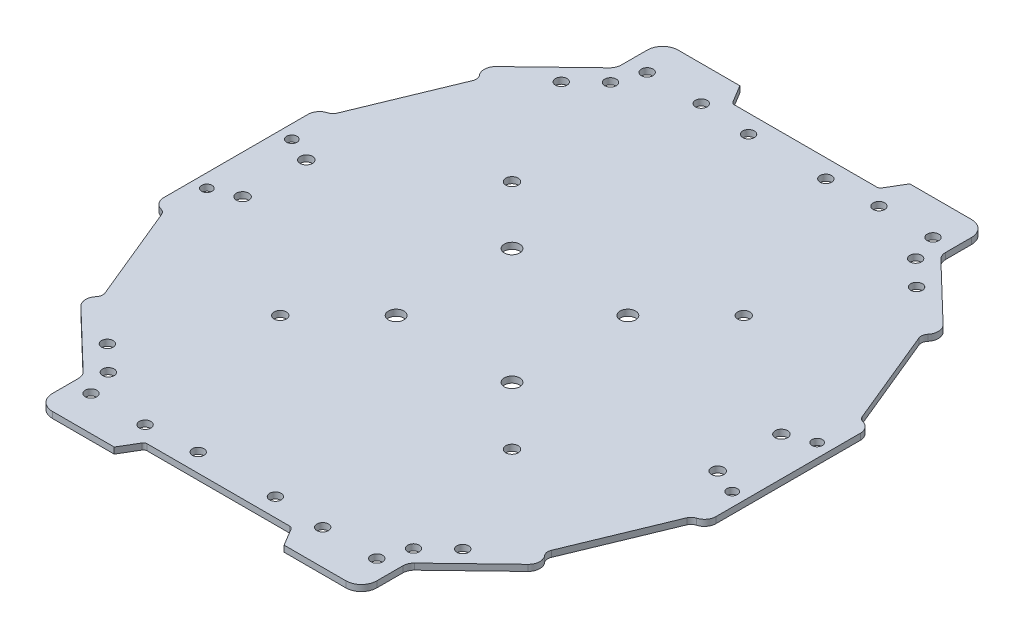
SolidWorks part; units mm, degrees
ref_plane "Front Plane" through (0, 0, 0) normal (0, 0, 1) x (1, 0, 0)
ref_plane "Top Plane" through (0, 0, 0) normal (0, 1, 0) x (1, 0, 0)
ref_plane "Right Plane" through (0, 0, 0) normal (1, 0, 0) x (0, 0, -1)
ref_plane "Plane1"
sketch "Sketch1" plane through (0, 0, 0) normal (0, 1, 0) x (-1, 0, 0)
  line L0 (59.7752, 259.0599) -> (56.7752, 264.0599)
  line L1 (56.7752, 264.0599) -> (36.7752, 264.0599)
  line L2 (36.7752, 264.0599) -> (36.7752, 252.0599)
  line L3 (36.7752, 252.0599) -> (18.7553, 234.7311)
  line L4 (18.7553, 234.7311) -> (21.5279, 231.8479)
  line L5 (21.5279, 231.8479) -> (10.2752, 204.5599)
  line L6 (10.2752, 204.5599) -> (7.2752, 204.5599)
  line L7 (7.2752, 204.5599) -> (7.2752, 183.0599)
  line L8 (7.2752, 183.0599) -> (7.2752, 161.5599)
  line L9 (7.2752, 161.5599) -> (10.2752, 161.5599)
  line L10 (10.2752, 161.5599) -> (21.5279, 134.2718)
  line L11 (21.5279, 134.2718) -> (18.7553, 131.3886)
  line L12 (18.7553, 131.3886) -> (36.7752, 114.0599)
  line L13 (36.7752, 114.0599) -> (36.7752, 102.0599)
  line L14 (36.7752, 102.0599) -> (56.7752, 102.0599)
  line L15 (56.7752, 102.0599) -> (59.7752, 107.0599)
  line L16 (59.7752, 107.0599) -> (78.7752, 107.0599)
  line L17 (78.7752, 107.0599) -> (97.7752, 107.0599)
  line L18 (97.7752, 107.0599) -> (100.7752, 102.0599)
  line L19 (100.7752, 102.0599) -> (120.7752, 102.0599)
  line L20 (120.7752, 102.0599) -> (120.7752, 114.0599)
  line L21 (120.7752, 114.0599) -> (138.795, 131.3886)
  line L22 (138.795, 131.3886) -> (136.0224, 134.2718)
  line L23 (136.0224, 134.2718) -> (147.2752, 161.5599)
  line L24 (147.2752, 161.5599) -> (150.2752, 161.5599)
  line L25 (150.2752, 161.5599) -> (150.2752, 183.0599)
  line L26 (150.2752, 183.0599) -> (150.2752, 204.5599)
  line L27 (150.2752, 204.5599) -> (147.2752, 204.5599)
  line L28 (147.2752, 204.5599) -> (136.0224, 231.8479)
  line L29 (136.0224, 231.8479) -> (138.795, 234.7311)
  line L30 (138.795, 234.7311) -> (120.7752, 252.0599)
  line L31 (120.7752, 252.0599) -> (120.7752, 264.0599)
  line L32 (120.7752, 264.0599) -> (100.7752, 264.0599)
  line L33 (100.7752, 264.0599) -> (97.7752, 259.0599)
  line L34 (97.7752, 259.0599) -> (78.7752, 259.0599)
  line L35 (78.7752, 259.0599) -> (59.7752, 259.0599)
  line L38 (78.7752, 259.0599) -> (78.7752, 107.0599) construction
  line L39 (150.2752, 183.0599) -> (7.2752, 183.0599) construction
  line L85 (91.8838, 199.6325) -> (91.9874, 199.5289)
  line L87 (95.3777, 196.1387) -> (95.4193, 196.097)
  circle A0 centre (55.7752, 111.0599) radius 1.5
  circle A1 centre (39.2752, 118.0599) radius 1.5
  circle A2 centre (48.7752, 213.0599) radius 1.6
  circle A3 centre (48.7752, 153.0599) radius 1.6
  circle A4 centre (17.2752, 174.8099) radius 1.6
  circle A5 centre (108.7752, 153.0599) radius 1.6
  circle A6 centre (93.7752, 198.0599) radius 2
  circle A7 centre (63.7752, 198.0599) radius 2
  circle A8 centre (63.7752, 168.0599) radius 2
  circle A9 centre (93.7752, 168.0599) radius 2
  circle A22 centre (41.7752, 255.0599) radius 1.5
  circle A23 centre (39.2752, 248.0599) radius 1.5
  circle A24 centre (10.7752, 194.0599) radius 1.35
  circle A25 centre (88.7752, 111.8099) radius 1.5
  circle A27 centre (115.7752, 111.0599) radius 1.5
  circle A28 centre (118.2752, 118.0599) radius 1.5
  circle A29 centre (140.2752, 174.8099) radius 1.6
  circle A30 centre (115.7752, 255.0599) radius 1.5
  circle A31 centre (88.7752, 254.3099) radius 1.5
  circle A32 centre (140.2752, 191.3099) radius 1.6
  circle A33 centre (146.7752, 194.0599) radius 1.35
  circle A53 centre (101.7752, 255.0599) radius 1.5
  circle A54 centre (118.2752, 248.0599) radius 1.5
  circle A55 centre (146.7752, 172.0599) radius 1.35
  circle A57 centre (101.7752, 111.0599) radius 1.5
  circle A69 centre (17.2752, 191.3099) radius 1.6
  circle A71 centre (55.7752, 255.0599) radius 1.5
  circle A73 centre (68.7752, 254.3099) radius 1.5
  circle A74 centre (10.7752, 172.0599) radius 1.35
  circle A76 centre (68.7752, 111.8099) radius 1.5
  circle A77 centre (41.7752, 111.0599) radius 1.5
  circle A82 centre (32.7752, 124.3099) radius 1.5
  circle A86 centre (124.7752, 241.8099) radius 1.5
  circle A87 centre (32.7752, 241.8099) radius 1.5
  circle A90 centre (108.7752, 213.0599) radius 1.6
  circle A91 centre (124.7752, 124.3099) radius 1.5
  point P41 (150.2752, 193.8099)
  dimension "D1" = 143
  dimension "D2" = 162
  dimension "D5" = 15
  dimension "D3" = 30
  dimension "D4" = 30
  dimension "D6" = 15
extrude "Extrusion1" add sketch "Sketch1" along normal blind 1.6
fillet "Fillet1" radius 1 4 edges at (-97.7752, 0.8, 107.0599) (-59.7752, 0.8, 107.0599) (-59.7752, 0.8, 259.0599) (-97.7752, 0.8, 259.0599)
fillet "Fillet2" radius 4 4 edges at (-120.7752, 0.8, 102.0599) (-36.7752, 0.8, 102.0599) (-120.7752, 0.8, 264.0599) (-36.7752, 0.8, 264.0599)
fillet "Fillet3" radius 3 4 edges at (-120.7752, 0.8, 114.0599) (-36.7752, 0.8, 114.0599) (-36.7752, 0.8, 252.0599) (-120.7752, 0.8, 252.0599)
fillet "Fillet4" radius 3 1 edges at (-138.795, 0.8, 234.7311)
fillet "Fillet5" radius 2 1 edges at (-136.0224, 0.8, 231.8479)
fillet "Fillet6" radius 2 1 edges at (-21.5279, 0.8, 231.8479)
fillet "Fillet7" radius 3 1 edges at (-18.7553, 0.8, 234.7311)
fillet "Fillet8" radius 3 2 edges at (-138.795, 0.8, 131.3886) (-18.7553, 0.8, 131.3886)
fillet "Fillet9" radius 2 2 edges at (-21.5279, 0.8, 134.2718) (-136.0224, 0.8, 134.2718)
fillet "Fillet10" radius 2 4 edges at (-10.2752, 0.8, 161.5599) (-10.2752, 0.8, 204.5599) (-147.2752, 0.8, 204.5599) (-147.2752, 0.8, 161.5599)
fillet "Fillet11" radius 3 4 edges at (-150.2752, 0.8, 161.5599) (-150.2752, 0.8, 204.5599) (-7.2752, 0.8, 204.5599) (-7.2752, 0.8, 161.5599)
